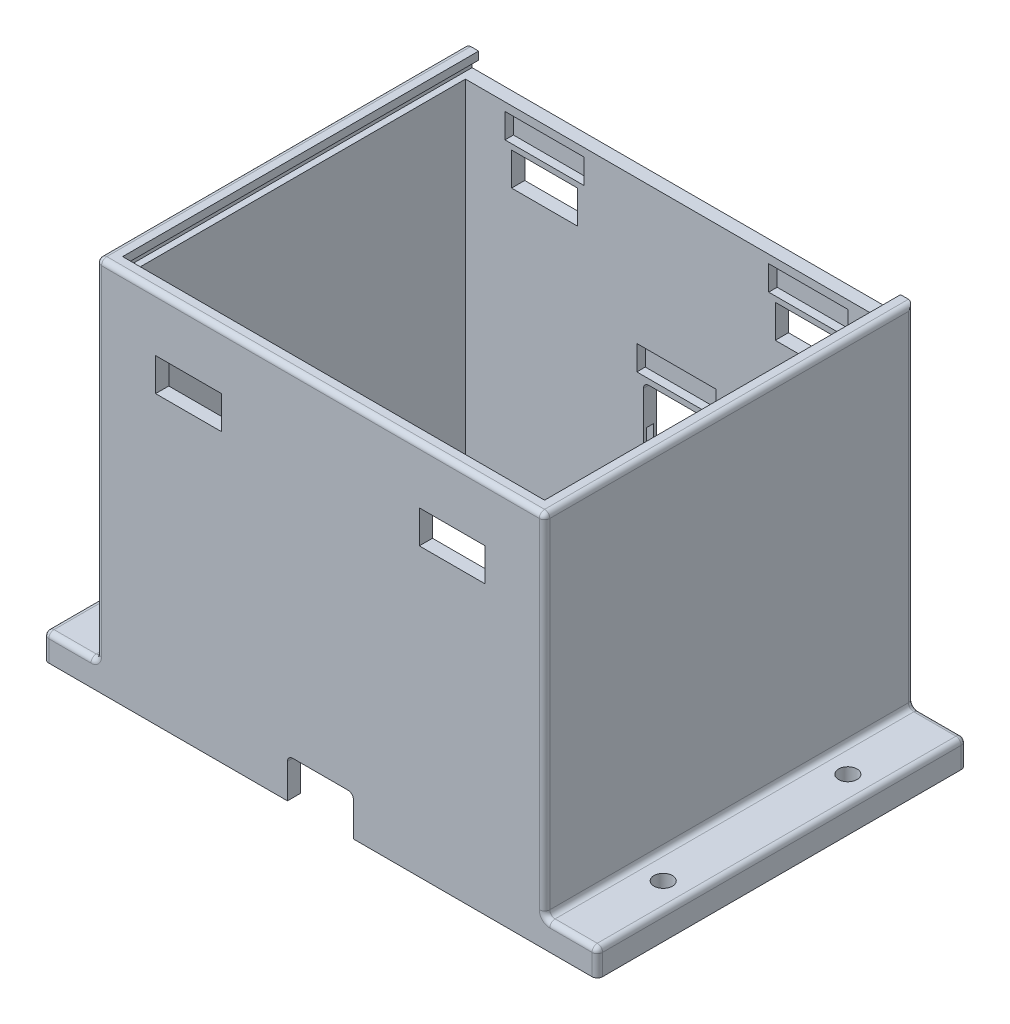
SolidWorks part; units mm, degrees
material "PLA"
ref_plane "Front Plane" through (0, 0, 0) normal (0, 0, 1) x (1, 0, 0)
ref_plane "Top Plane" through (0, 0, 0) normal (0, 1, 0) x (1, 0, 0)
ref_plane "Right Plane" through (0, 0, 0) normal (1, 0, 0) x (0, 0, -1)
sketch "Sketch1" plane through (0, 0, 0) normal (1, 0, 0) x (0, 0, -1)
  line L0 (55, 0) -> (-55, 0) construction
  line L5 (90, 142.5) -> (90, 0)
  line L14 (85, 137.5) -> (85, 0)
  line L17 (-50, 0) -> (-45, 0)
  line L18 (-45, 137.5) -> (-45, 0)
  line L20 (85, 137.5) -> (85, 0)
  line L21 (85, 0) -> (90, 0)
  line L23 (-50, 142.5) -> (90, 142.5)
  line L27 (-50, 142.5) -> (-50, 0)
  line L28 (-50, 142.5) -> (90, 142.5)
  line L29 (-45, 137.5) -> (85, 137.5)
  dimension "D1" = 5
  dimension "D3" = 142.5
  dimension "D5" = 5
extrude "Boss-Extrude1" add sketch "Sketch1" along normal blind 170
ref_plane "Plane1" through (0, 0, -90) normal (0, 0, 1) x (1, 0, 0)
ref_plane "Plane2" through (0, 0, 45) normal (0, 0, -1) x (-1, 0, 0)
sketch "Sketch7" plane through (0, 0, 45) normal (0, 0, -1) x (-1, 0, 0)
  line L0 (-85, 0) -> (-85, 142.5) construction
  line L5 (-170, 0) -> (0, 0) construction
  line L6 (-170, 142.5) -> (0, 142.5) construction
  line L7 (-165, 0) -> (-170, 0)
  line L8 (-170, 0) -> (-170, 142.5)
  line L9 (-165, 0) -> (-165, 142.5)
  line L10 (-165, 142.5) -> (-170, 142.5)
  line L11 (-5, 142.5) -> (0, 142.5)
  line L12 (-5, 0) -> (-5, 142.5)
  line L13 (0, 0) -> (0, 142.5)
  line L14 (-5, 0) -> (0, 0)
  dimension "D1" = 5
  dimension "D2" = 142.5
  dimension "D3" = 80
extrude "Boss-Extrude2" add sketch "Sketch7" along normal blind 130
ref_plane "Plane3" through (0, 122.5, 0) normal (0, 1, 0) x (1, 0, 0)
sketch "Sketch9" plane through (0, 142.5, 0) normal (0, 1, 0) x (1, 0, 0)
  line L0 (170, -50) -> (0, -50) construction
  line L1 (170, -50) -> (170, 90) construction
  line L4 (165, -45) -> (5, -45)
  line L5 (165, -45) -> (165, 85)
  line L6 (165, 85) -> (5, 85)
  line L7 (5, -45) -> (5, 85)
  line L8 (165, -45) -> (5, 85) construction
  line L9 (165, 85) -> (5, -45) construction
  point P6 (85, 20)
  dimension "D1" = 160
  dimension "D2" = 130
  dimension "D3" = 70
  dimension "D4" = 85
extrude "Cut-Extrude2" cut sketch "Sketch9" against normal blind 60
sketch "Sketch10" plane through (80, 0, -90) normal (0, 0, 1) x (1, 0, 0)
  line L1 (-77.5, 139.5) -> (87.5, 139.5)
  line L2 (-77.5, 139.5) -> (-77.5, 135.8)
  line L3 (-77.5, 135.8) -> (87.5, 135.8)
  line L4 (87.5, 139.5) -> (87.5, 135.8)
  line L10 (-80, 142.5) -> (-80, 0) construction
  line L11 (90, 142.5) -> (-80, 142.5) construction
  point P6 (5, 135.8)
  dimension "D1" = 3.7
  dimension "D2" = 3
  dimension "D3" = 165
  dimension "D4" = 85
extrude "Cut-Extrude3" cut sketch "Sketch10" along normal blind 137.5
ref_plane "Plane4" through (170, 0, 0) normal (1, 0, 0) x (0, 0, -1)
sketch "Sketch13" plane through (80, 0, -90) normal (0, 0, 1) x (1, 0, 0)
  line L6 (87.5, 139.5) -> (-77.5, 139.5) construction
  line L7 (-75, 142.5) -> (85, 142.5)
  line L8 (-75, 142.5) -> (-75, 136.5)
  line L9 (-75, 136.5) -> (85, 136.5)
  line L10 (85, 142.5) -> (85, 136.5)
  line L11 (-75, 142.5) -> (85, 136.5) construction
  line L12 (-75, 136.5) -> (85, 142.5) construction
  line L13 (90, 142.5) -> (90, 0) construction
  point P4 (5, 139.5)
  dimension "D1" = 85
  dimension "D2" = 160
  dimension "D3" = 6
extrude "Cut-Extrude4" cut sketch "Sketch13" along normal blind 5
ref_plane "Plane5" through (0, 0, -20) normal (0, 0, 1) x (1, 0, 0)
sketch "Sketch15" plane through (0, 0, -20) normal (0, 0, 1) x (1, 0, 0)
  line L0 (85, 0) -> (85, 142.5) construction
  line L1 (0, 0) -> (-20, 0)
  line L2 (0, 0) -> (0, 10)
  line L3 (0, 10) -> (-20, 10)
  line L4 (-20, 0) -> (-20, 10)
  line L5 (170, 0) -> (0, 0) construction
  line L6 (170, 142.5) -> (0, 142.5) construction
  line L7 (190, 0) -> (190, 10)
  line L8 (170, 10) -> (190, 10)
  line L9 (170, 0) -> (170, 10)
  line L10 (170, 0) -> (190, 0)
  dimension "D1" = 10
  dimension "D2" = 20
extrude "Boss-Extrude3" add sketch "Sketch15" along normal mid plane 140
sketch "Sketch16" plane through (0, 0, 50) normal (0, 0, 1) x (1, 0, 0)
  line L0 (0, 142.5) -> (0, 10) construction
  line L1 (22.5, 108.75) -> (47.5, 108.75)
  line L2 (22.5, 108.75) -> (22.5, 121.25)
  line L3 (22.5, 121.25) -> (47.5, 121.25)
  line L4 (47.5, 108.75) -> (47.5, 121.25)
  line L5 (22.5, 108.75) -> (47.5, 121.25) construction
  line L6 (22.5, 121.25) -> (47.5, 108.75) construction
  line L7 (85, 142.5) -> (85, 0) construction
  line L8 (170, 142.5) -> (0, 142.5) construction
  line L9 (190, 0) -> (-20, 0) construction
  line L10 (147.5, 121.25) -> (122.5, 108.75) construction
  line L11 (147.5, 108.75) -> (122.5, 121.25) construction
  line L12 (122.5, 108.75) -> (122.5, 121.25)
  line L13 (147.5, 121.25) -> (122.5, 121.25)
  line L14 (147.5, 108.75) -> (147.5, 121.25)
  line L15 (147.5, 108.75) -> (122.5, 108.75)
  point P0 (35, 115)
  point P17 (135, 115)
  dimension "D1" = 35
  dimension "D2" = 12.5
  dimension "D3" = 115
  dimension "D4" = 25
extrude "Cut-Extrude5" cut sketch "Sketch16" against normal blind 5
hole_wizard "M6 Clearance Hole1" positions "Sketch20" profile "Sketch21" hole size "M6" standard "ANSI Metric" end condition up to next
sketch "Sketch20" plane through (0, 10, 0) normal (0, 1, 0) x (1, 0, 0)
  line L0 (190, -50) -> (190, 90) construction
  point P0 (-10, -15)
  point P2 (-10, 55)
  point P4 (180, 55)
  point P6 (180, -15)
  dimension "D1" = 10
  dimension "D2" = 10
  dimension "D3" = 35
  dimension "D4" = 105
sketch "Sketch21" plane through (-10, 10, 15) normal (1, 0, 0) x (0, 0, 1)
  line L0 (0, 0) -> (0, 10)
  line L1 (0, 10) -> (3.5, 10)
  line L2 (3.5, 10) -> (3.5, 0)
  line L5 (3.5, 0) -> (0, 0)
  line L11 (0, -6.35) -> (0, 107.95) construction
  dimension "Thru Hole Dia." = 7
  dimension "Thru Hole Depth" = 10
ref_plane "Plane6" through (35, 0, 0) normal (1, 0, 0) x (0, 0, -1)
ref_plane "Center Plane" through (85, 0, 0) normal (1, 0, 0) x (0, 0, -1)
mirror "Mirror2" about plane through (0, 0, -20) normal (0, 0, 1) of "Cut-Extrude5"
sketch "Sketch26" plane through (0, 0, -20) normal (0, 0, 1) x (1, 0, 0)
  line L1 (150, 123.325) -> (120, 123.325)
  line L2 (150, 123.325) -> (150, 132.675)
  line L3 (150, 132.675) -> (120, 132.675)
  line L4 (120, 123.325) -> (120, 132.675)
  line L5 (150, 123.325) -> (120, 132.675) construction
  line L6 (150, 132.675) -> (120, 123.325) construction
  line L7 (50, 132.675) -> (20, 132.675)
  line L8 (50, 132.675) -> (50, 123.325)
  line L9 (50, 123.325) -> (20, 123.325)
  line L10 (20, 132.675) -> (20, 123.325)
  line L11 (50, 132.675) -> (20, 123.325) construction
  line L12 (50, 123.325) -> (20, 132.675) construction
  line L16 (35, -77) -> (35, 77) construction
  line L17 (190, 0) -> (-20, 0) construction
  point P0 (135, 128)
  point P5 (35, 128)
  dimension "D1" = 100
  dimension "D2" = 30
  dimension "D3" = 9.35
  dimension "D4" = 128
extrude "Cut-Extrude6" cut sketch "Sketch26" against normal mid plane 136.4
sketch "Sketch27" plane through (0, 0, -20) normal (0, 0, 1) x (1, 0, 0)
  line L0 (190, 0) -> (-20, 0) construction
  line L1 (-20, 10) -> (-20, 0) construction
  line L2 (70, 17.125) -> (100, 17.125)
  line L3 (70, 17.125) -> (70, 26.475)
  line L4 (70, 26.475) -> (100, 26.475)
  line L5 (100, 17.125) -> (100, 26.475)
  line L6 (70, 17.125) -> (100, 26.475) construction
  line L7 (70, 26.475) -> (100, 17.125) construction
  point P4 (85, 21.8)
  dimension "D1" = 30
  dimension "D2" = 9.35
  dimension "D3" = 105
  dimension "D4" = 21.8
extrude "Cut-Extrude8" cut sketch "Sketch27" along normal blind 68.2
ref_plane "Plane8" through (0, 0, 50) normal (0, 0, -1) x (-1, 0, 0)
sketch "Sketch28" plane through (0, 0, 50) normal (0, 0, -1) x (-1, 0, 0)
  line L0 (-72.5, 0) -> (-72.5, 13)
  line L1 (-190, 0) -> (20, 0) construction
  line L2 (-74.5, 15) -> (-95.5, 15)
  line L3 (-97.5, 13) -> (-97.5, 0)
  line L4 (-72.5, 0) -> (-97.5, 0)
  arc A0 (-95.5, 15) -> (-97.5, 13) centre (-95.5, 13) ccw
  arc A1 (-72.5, 13) -> (-74.5, 15) centre (-74.5, 13) ccw
  point P4 (-85, 0)
  point P9 (-97.5, 15)
  point P12 (-72.5, 15)
  dimension "D4" = 2
  dimension "D1" = 15
  dimension "D2" = 25
  dimension "D3" = 12.5
extrude "Cut-Extrude10" cut sketch "Sketch28" along normal blind 5
sketch "Sketch29" plane through (0, 0, -90) normal (0, 0, 1) x (1, 0, 0)
  line L0 (190, 0) -> (-20, 0) construction
  line L3 (190, 0) -> (190, 10) construction
  line L4 (95.5, 52.5) -> (74.5, 52.5)
  line L5 (97.5, 54.5) -> (97.5, 68)
  line L6 (95.5, 70) -> (74.5, 70)
  line L7 (72.5, 54.5) -> (72.5, 68)
  line L8 (97.5, 52.5) -> (72.5, 70) construction
  line L9 (97.5, 70) -> (72.5, 52.5) construction
  arc A0 (72.5, 54.5) -> (74.5, 52.5) centre (74.5, 54.5) ccw
  arc A1 (74.5, 70) -> (72.5, 68) centre (74.5, 68) ccw
  arc A2 (97.5, 54.5) -> (95.5, 52.5) centre (95.5, 54.5) cw
  arc A3 (97.5, 68) -> (95.5, 70) centre (95.5, 68) ccw
  point P2 (85, 0)
  point P6 (85, 61.25)
  dimension "D3" = 2
  dimension "D1" = 25
  dimension "D2" = 17.5
  dimension "D4" = 61.25
  dimension "D5" = 105
extrude "Cut-Extrude11" cut sketch "Sketch29" along normal blind 5
sketch "Sketch30" plane through (0, 0, -20) normal (0, 0, 1) x (1, 0, 0)
  line L0 (190, 0) -> (190, 10) construction
  line L1 (100, 81.475) -> (70, 81.475)
  line L2 (100, 81.475) -> (100, 72.125)
  line L3 (100, 72.125) -> (70, 72.125)
  line L4 (70, 81.475) -> (70, 72.125)
  line L5 (100, 81.475) -> (70, 72.125) construction
  line L6 (100, 72.125) -> (70, 81.475) construction
  line L7 (190, 0) -> (-20, 0) construction
  point P0 (85, 76.8)
  point P9 (85, 0)
  dimension "D1" = 9.35
  dimension "D2" = 30
  dimension "D3" = 105
  dimension "D4" = 76.8
extrude "Cut-Extrude12" cut sketch "Sketch30" against normal blind 68.2
sketch "Sketch31" plane through (0, 0, 0) normal (0, 1, 0) x (1, 0, 0)
  line L0 (165, 85) -> (5, 85) construction
  line L3 (97.5, 86.25) -> (100.5, 86.25)
  line L4 (97.5, 85) -> (72.5, 85)
  line L5 (97.5, 85) -> (97.5, 86.25)
  line L6 (97.5, 90) -> (72.5, 90)
  line L7 (72.5, 85) -> (72.5, 86.25)
  line L8 (97.5, 85) -> (72.5, 90) construction
  line L9 (97.5, 90) -> (72.5, 85) construction
  line L11 (97.5, 88.75) -> (100.5, 88.75)
  line L12 (100.5, 86.25) -> (100.5, 88.75)
  line L13 (97.5, 88.75) -> (97.5, 90)
  line L14 (85, 85) -> (85, 90) construction
  line L18 (72.5, 88.75) -> (72.5, 90)
  line L19 (190, -50) -> (190, 90) construction
  line L20 (72.5, 86.25) -> (69.5, 86.25)
  line L21 (69.5, 86.25) -> (69.5, 88.75)
  line L22 (72.5, 88.75) -> (69.5, 88.75)
  point P6 (85, 87.5)
  point P12 (85, 85)
  dimension "D1" = 25
  dimension "D2" = 5
  dimension "D3" = 2.5
  dimension "D4" = 2.5
  dimension "D5" = 3
  dimension "D6" = 105
  dimension "D9" = 1.25
extrude "Cut-Extrude14" cut sketch "Sketch31" along normal blind 54.5
fillet "Fillet1" radius 2 19 edges at (180, 10, -90) (180, 10, 50) (-10, 10, -90) (-10, 10, 50) (170, 142.5, -20) (85, 142.5, 50) (0, 142.5, -20) (190, 10, -20) (170, 10, -20) (-20, 10, -20) (0, 10, -20) (0, 76.25, 50) (170, 76.25, 50) (0, 76.25, -90) (170, 76.25, -90) (190, 5, -90) (190, 5, 50) (-20, 5, -90) (-20, 5, 50)
